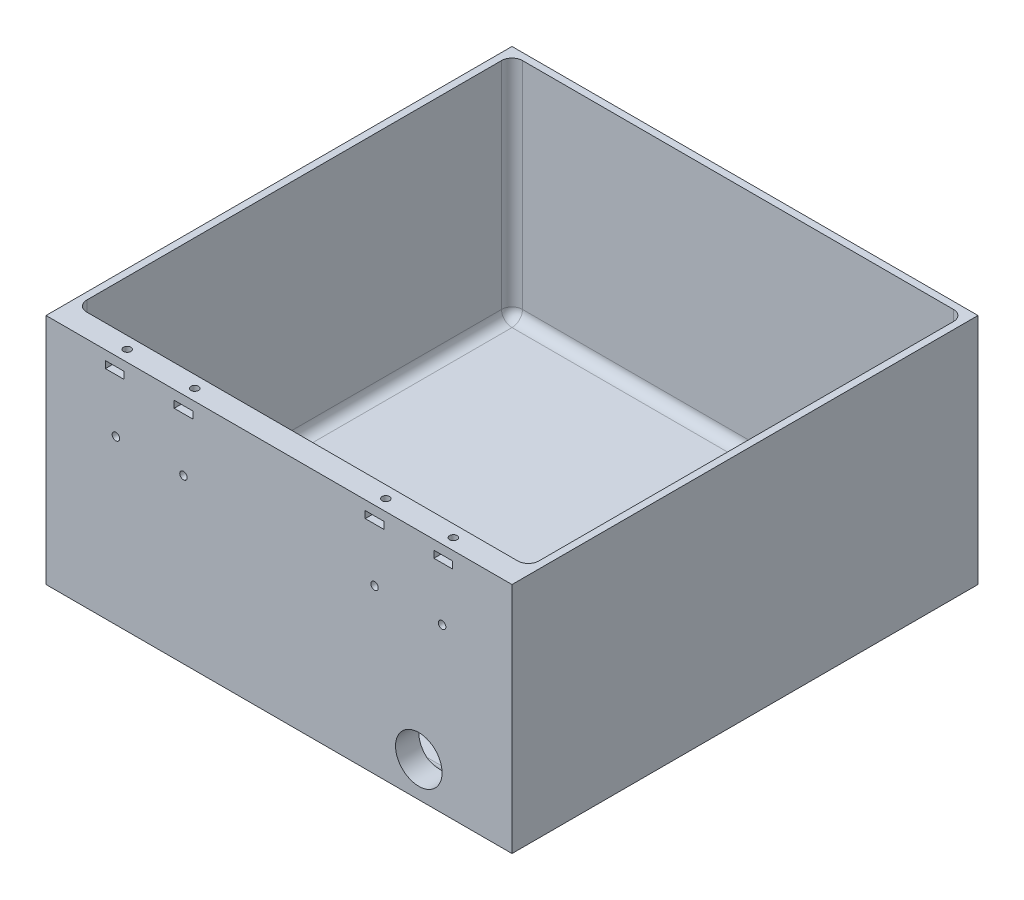
SolidWorks part; units mm, degrees
ref_plane "Alzado" through (0, 0, 0) normal (0, 0, 1) x (1, 0, 0)
ref_plane "Planta" through (0, 0, 0) normal (0, 1, 0) x (1, 0, 0)
ref_plane "Vista lateral" through (0, 0, 0) normal (1, 0, 0) x (0, 0, -1)
sketch "Croquis1" plane through (0, 0, 0) normal (0, 1, 0) x (1, 0, 0)
  line L1 (100, -100) -> (-100, -100)
  line L2 (100, -100) -> (100, 100)
  line L3 (100, 100) -> (-100, 100)
  line L4 (-100, -100) -> (-100, 100)
  line L5 (100, -100) -> (-100, 100) construction
  line L6 (100, 100) -> (-100, -100) construction
  point P0 (0, 0)
  dimension "D1" = 200
  dimension "D2" = 200
extrude "Saliente-Extruir1" add sketch "Croquis1" along normal blind 100
sketch "Croquis2" plane through (0, 100, 0) normal (0, 1, 0) x (1, 0, 0)
  line L0 (-100, 100) -> (-100, -100) construction
  line L1 (-97, 97) -> (97, 97)
  line L2 (-97, 97) -> (-97, -90)
  line L3 (-97, -90) -> (97, -90)
  line L4 (97, 97) -> (97, -90)
  line L5 (-97, 97) -> (97, -90) construction
  line L6 (-97, -90) -> (97, 97) construction
  line L7 (100, 100) -> (-100, 100) construction
  line L8 (100, -100) -> (100, 100) construction
  line L9 (-100, -100) -> (100, -100) construction
  point P4 (0, 3.5)
  dimension "D1" = 3
  dimension "D2" = 3
  dimension "D3" = 3
  dimension "D4" = 10
extrude "Cortar-Extruir1" cut sketch "Croquis2" against normal offset from surface (97 mm away) 3 up to face at (0, 0, 0)
fillet "Redondeo2" radius 4.5 8 edges at (0, 3, -97) (97, 3, -3.5) (0, 3, 90) (-97, 3, -3.5) (97, 51.5, 90) (-97, 51.5, 90) (97, 51.5, -97) (-97, 51.5, -97)
sketch "Croquis3" plane through (0, 0, 100) normal (0, 0, 1) x (1, 0, 0)
  line L0 (-100, 100) -> (100, 100) construction
  line L1 (-74.5, 96) -> (-66.5, 96)
  line L2 (-74.5, 96) -> (-74.5, 93)
  line L3 (-74.5, 93) -> (-66.5, 93)
  line L4 (-66.5, 96) -> (-66.5, 93)
  line L5 (-74.5, 96) -> (-66.5, 93) construction
  line L6 (-74.5, 93) -> (-66.5, 96) construction
  line L7 (-100, 100) -> (-100, 0) construction
  line L9 (-45, 96) -> (-37, 96)
  line L10 (-45, 96) -> (-45, 93)
  line L11 (-45, 93) -> (-37, 93)
  line L12 (-37, 96) -> (-37, 93)
  line L13 (-45, 96) -> (-37, 93) construction
  line L14 (-45, 93) -> (-37, 96) construction
  circle A0 centre (-70, 70) radius 1.6
  circle A1 centre (-41, 70) radius 1.6
  point P4 (-70.5, 94.5)
  point P13 (-41, 94.5)
  dimension "D8" = 3.2
  dimension "D9" = 3.2
  dimension "D10" = 59
  dimension "D11" = 30
  dimension "D13" = 30
  dimension "D1" = 3
  dimension "D2" = 8
  dimension "D3" = 4
  dimension "D4" = 25.5
  dimension "D5" = 8
  dimension "D6" = 3
  dimension "D7" = 55
  dimension "D12" = 30
extrude "Cortar-Extruir2" cut sketch "Croquis3" against normal up to next (10 mm away)
mirror "Simetría1" about plane through (0, 0, 0) normal (1, 0, 0) of "Cortar-Extruir2"
sketch "Croquis4" plane through (0, 0, 100) normal (0, 0, 1) x (1, 0, 0)
  line L0 (-100, 0) -> (100, 0) construction
  line L1 (100, 100) -> (100, 0) construction
  circle A0 centre (60, 15) radius 10
  dimension "D1" = 20
  dimension "D2" = 15
  dimension "D3" = 40
extrude "Cortar-Extruir3" cut sketch "Croquis4" against normal up to next
sketch "Croquis5" plane through (0, 100, 0) normal (0, 1, 0) x (1, 0, 0)
  line L0 (-100, 100) -> (-100, -100) construction
  circle A0 centre (-70, -95.1593) radius 1.6
  circle A1 centre (-41, -95.1593) radius 1.6
  dimension "D1" = 3.2
  dimension "D2" = 3.2
  dimension "D4" = 59
  dimension "D3" = 30
extrude "Cortar-Extruir4" cut sketch "Croquis5" against normal up to surface (4 mm away) up to face at (-70.5, 96, 95)
mirror "Simetría2" about plane through (0, 0, 0) normal (1, 0, 0) of "Cortar-Extruir4"
